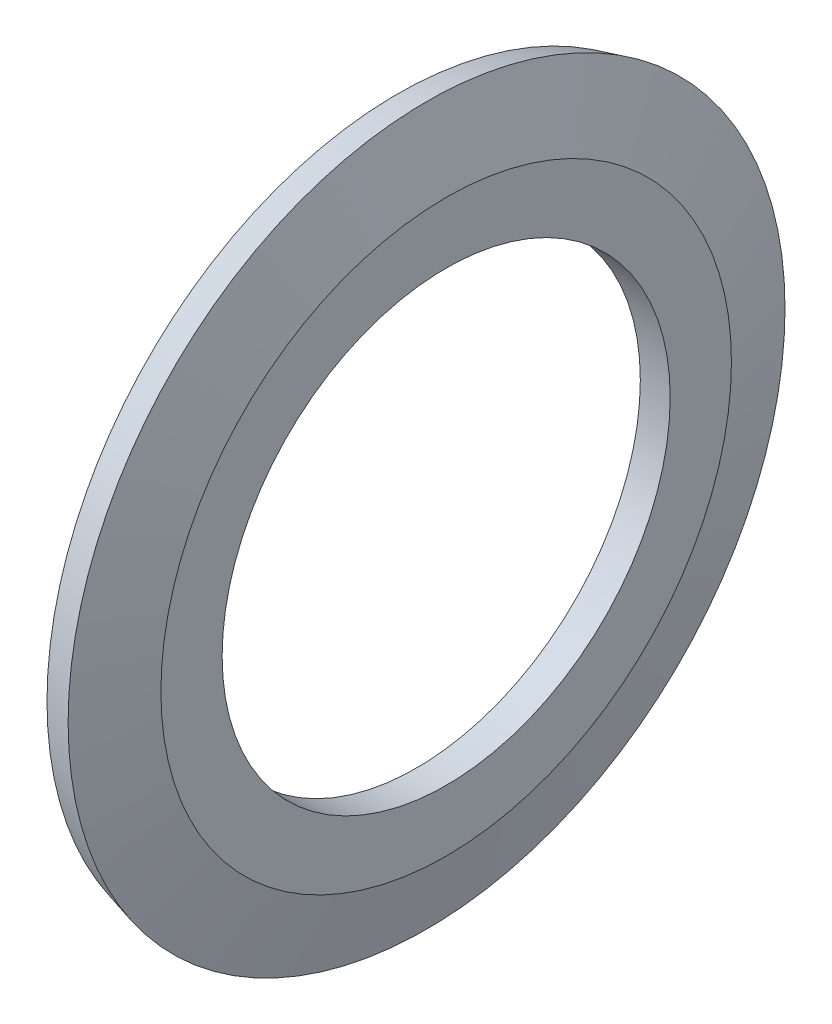
SolidWorks part; units mm, degrees
ref_plane "Front Plane" through (0, 0, 0) normal (0, 0, 1) x (1, 0, 0)
ref_plane "Top Plane" through (0, 0, 0) normal (0, 1, 0) x (1, 0, 0)
ref_plane "Right Plane" through (0, 0, 0) normal (1, 0, 0) x (0, 0, -1)
sketch "Sketch1" plane through (0, 0, 0) normal (0, 0, 1) x (1, 0, 0)
  line L0 (0, 0) -> (1, 0) construction
  line L1 (0, 7.5) -> (0, 9.4183)
  line L2 (0, 9.4183) -> (-0.6224, 11.7412)
  line L3 (1, 7.5) -> (1, 9.55)
  line L4 (1, 9.55) -> (0.3435, 12)
  line L5 (0, 7.5) -> (1, 7.5)
  line L8 (-0.6224, 11.7412) -> (0.3435, 12)
  dimension "D2" = 15
  dimension "F" = 24
  dimension "E" = 15
  dimension "MSM_12" = 1
  dimension "P.D." = 19.1
revolve "Revolve1" add sketch "Sketch1" angle 360 about L0
sketch "Sketch2" [suppressed] plane through (0, 0, 0) normal (0, 0, 1) x (1, 0, 0)
  line L0 (0, 0) -> (0.5753, 0) construction
  line L1 (0, 15.7833) -> (0, -15.7833) construction
  line L3 (0.5753, 17.2412) -> (0, 17.2412)
  line L4 (0.5753, 17.2412) -> (0.5753, 15)
  line L5 (0.5753, 15) -> (0, 15)
  line L6 (0, 17.2412) -> (0, 15)
  line L7 (0.5753, 17.5) -> (0.5753, -17.5) construction
  dimension "FC" = 31
revolve "Cut-Revolve1" [suppressed] cut sketch "Sketch2" angle 360 about L0
